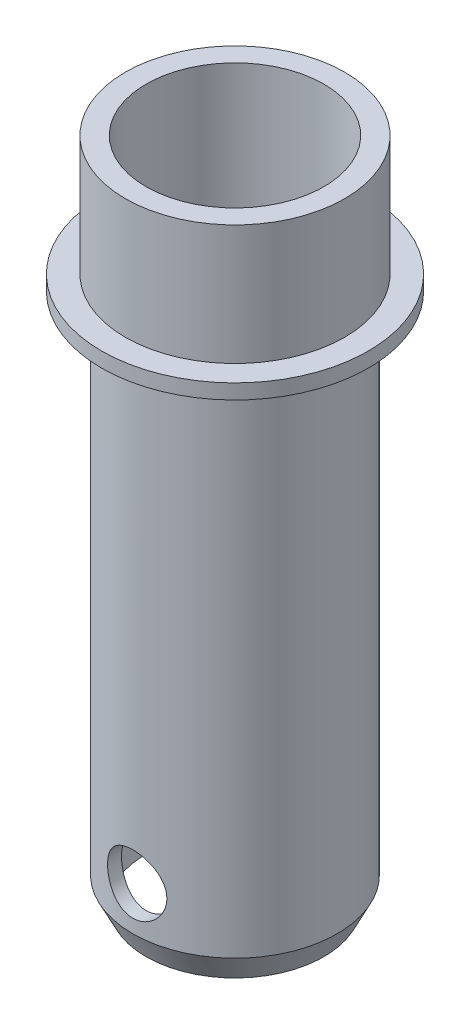
SolidWorks part; units mm, degrees
ref_plane "Спереди" through (0, 0, 0) normal (0, 0, 1) x (1, 0, 0)
ref_plane "Сверху" through (0, 0, 0) normal (0, 1, 0) x (1, 0, 0)
ref_plane "Справа" through (0, 0, 0) normal (1, 0, 0) x (0, 0, -1)
sketch "Эскиз1" plane through (0, 0, 0) normal (0, 0, 1) x (1, 0, 0)
  line L0 (0, 30.7123) -> (0, -29.2039) construction
  line L1 (-7.4, 9.1) -> (-7.4, 1)
  line L2 (-6, 9.1) -> (-7.4, 9.1)
  line L3 (-7.4, 1) -> (-9, 1)
  line L4 (-9, 1) -> (-9, 0)
  line L5 (-9, 0) -> (-6.8941, 0)
  line L6 (-6.8941, 0) -> (-6.8941, -34.111)
  line L7 (-6.8941, -34.111) -> (-6, -35.9)
  line L8 (-6, -35.9) -> (-6, 9.1)
  dimension "D1" = 45
  dimension "D2" = 8.1
  dimension "D3" = 6
  dimension "D4" = 7.4
  dimension "D5" = 9
  dimension "D6" = 1
  dimension "D7" = 2
  dimension "D8" = 34.111
revolve "Повернуть1" add sketch "Эскиз1" angle 360 about L0
sketch "Эскиз2" plane through (0, 0, 0) normal (0, 0, 1) x (1, 0, 0)
  line L0 (6, -35.9) -> (-6, -35.9) construction
  circle A0 centre (0, -31.2) radius 2
  dimension "D1" = 4
  dimension "D2" = 4.7
extrude "Вырез-Вытянуть1" cut sketch "Эскиз2" against normal through all both and the other way through all
